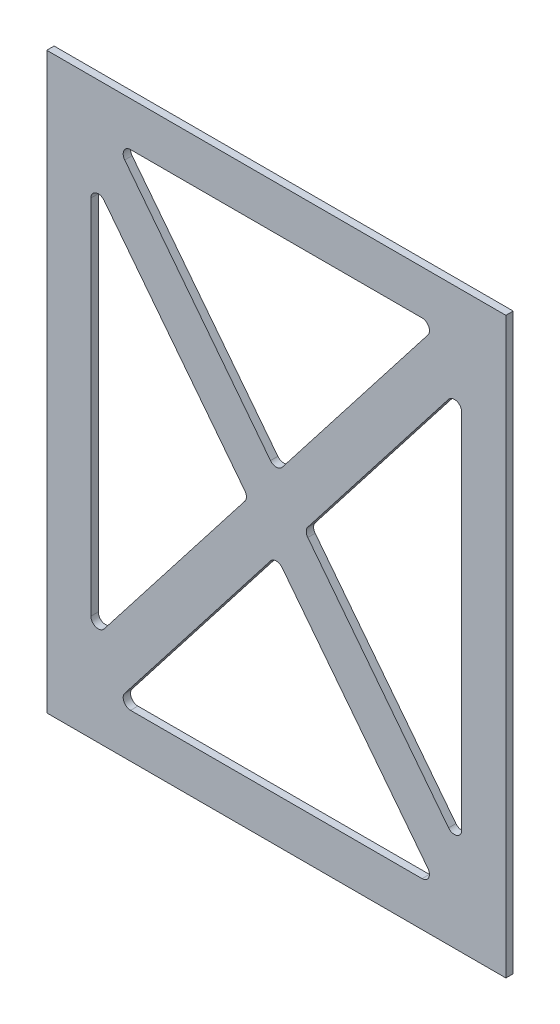
SolidWorks part; units mm, degrees
ref_plane "Front Plane" through (0, 0, 0) normal (0, 0, 1) x (1, 0, 0)
ref_plane "Top Plane" through (0, 0, 0) normal (0, 1, 0) x (1, 0, 0)
ref_plane "Right Plane" through (0, 0, 0) normal (1, 0, 0) x (0, 0, -1)
sketch "Sketch1" plane through (0, 0, 0) normal (0, 0, 1) x (1, 0, 0)
  line L1 (-99.06, -123.825) -> (99.06, -123.825)
  line L2 (-99.06, -123.825) -> (-99.06, 123.825)
  line L3 (-99.06, 123.825) -> (99.06, 123.825)
  line L4 (99.06, -123.825) -> (99.06, 123.825)
  line L5 (-99.06, -123.825) -> (99.06, 123.825) construction
  line L6 (-99.06, 123.825) -> (99.06, -123.825) construction
  point P0 (0, 0)
  dimension "D1" = 198.12
  dimension "D2" = 247.65
extrude "Boss-Extrude1" add sketch "Sketch1" along normal blind 3.175
sketch "Sketch2" plane through (0, 0, 3.175) normal (0, 0, 1) x (1, 0, 0)
  line L0 (-69.3934, 104.775) -> (80.01, -87.3935)
  line L1 (-80.01, -104.775) -> (80.01, -104.775)
  line L2 (-80.01, -104.775) -> (-80.01, 104.775)
  line L3 (-80.01, 104.775) -> (80.01, 104.775)
  line L4 (99.06, -123.825) -> (99.06, 123.825)
  line L5 (99.06, 123.825) -> (-99.06, 123.825)
  line L6 (-99.06, 123.825) -> (-99.06, -123.825)
  line L7 (-99.06, -123.825) -> (99.06, -123.825)
  line L8 (99.06, -123.825) -> (99.06, 123.825)
  line L9 (99.06, 123.825) -> (-99.06, 123.825)
  line L10 (-99.06, 123.825) -> (-99.06, -123.825)
  line L11 (-99.06, -123.825) -> (99.06, -123.825)
  line L12 (80.01, -104.775) -> (80.01, 104.775)
  line L13 (-80.01, -104.775) -> (80.01, 104.775) construction
  line L14 (-80.01, 104.775) -> (80.01, -104.775) construction
  line L15 (-80.01, 87.3935) -> (69.3934, -104.775)
  line L16 (-80.01, -87.3935) -> (69.3934, 104.775)
  line L17 (-69.3934, -104.775) -> (80.01, 87.3935)
  point P2 (0, 0)
  point P18 (-12.065, 0)
  point P19 (0, 15.5185)
  point P20 (12.065, 0)
  point P21 (0, 0)
  point P22 (0, 0)
  point P23 (0, 0)
  point P24 (0, 0)
  point P25 (0, 0)
  point P26 (0, 0)
  point P27 (0, 0)
  dimension "D2" = 19.05
  dimension "D3" = 19.05
  dimension "D4" = 19.05
  dimension "D5" = 19.05
  dimension "D6" = 24.13
  dimension "D1" = 0
extrude "Cut-Extrude1" cut sketch "Sketch2" against normal up to next
fillet "Fillet1" radius 3.175 12 edges at (69.3934, -104.775, 1.5875) (80.01, -87.3935, 1.5875) (0, -15.5185, 1.5875) (-69.3934, -104.775, 1.5875) (-80.01, -87.3935, 1.5875) (80.01, 87.3935, 1.5875) (69.3934, 104.775, 1.5875) (12.065, 0, 1.5875) (-12.065, 0, 1.5875) (0, 15.5185, 1.5875) (-69.3934, 104.775, 1.5875) (-80.01, 87.3935, 1.5875)
